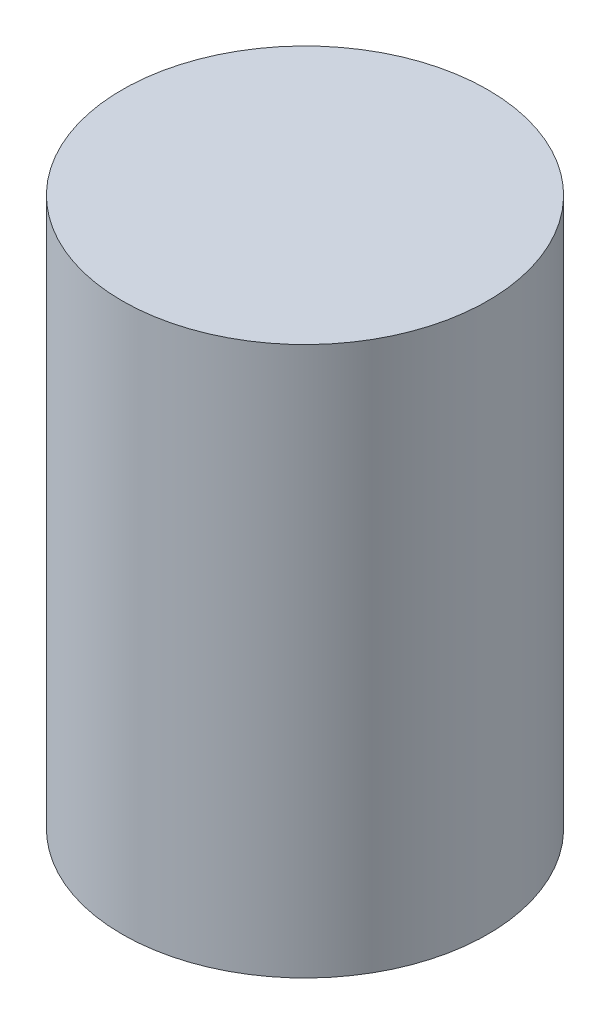
SolidWorks part; units mm, degrees
ref_plane "Front Plane" through (0, 0, 0) normal (0, 0, 1) x (1, 0, 0)
ref_plane "Top Plane" through (0, 0, 0) normal (0, 1, 0) x (1, 0, 0)
ref_plane "Right Plane" through (0, 0, 0) normal (1, 0, 0) x (0, 0, -1)
sketch "Sketch1" plane through (0, 0, 0) normal (0, 1, 0) x (1, 0, 0)
  circle A0 centre (0, 0) radius 10
  dimension "20" = 20
extrude "Boss-Extrude1" add sketch "Sketch1" along normal blind 30
